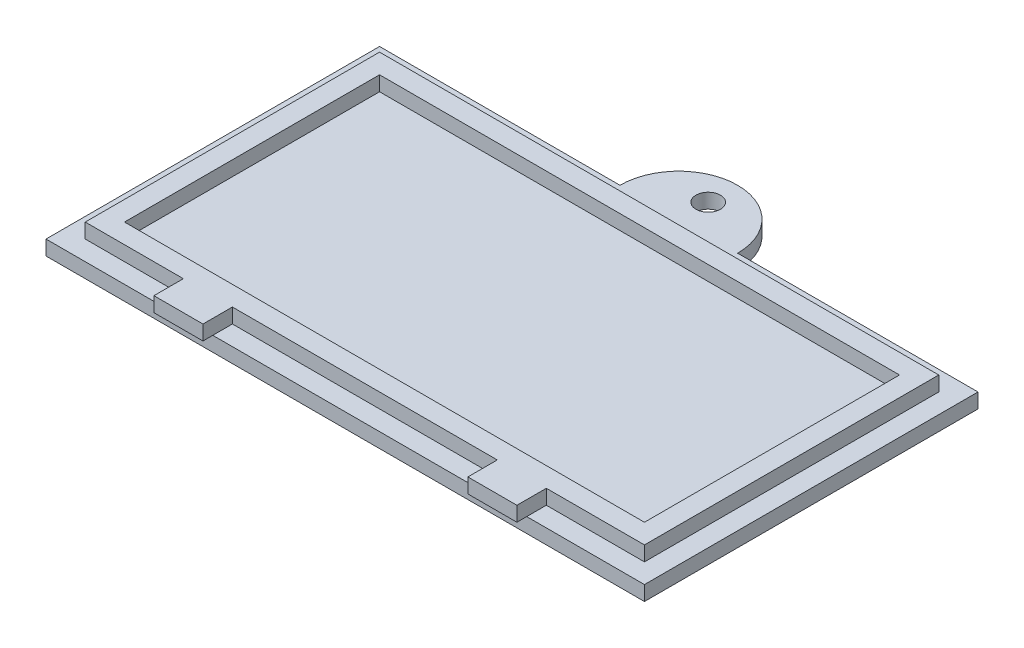
SolidWorks part; units mm, degrees
ref_plane "Front Plane" through (0, 0, 0) normal (0, 0, 1) x (1, 0, 0)
ref_plane "Top Plane" through (0, 0, 0) normal (0, 1, 0) x (1, 0, 0)
ref_plane "Right Plane" through (0, 0, 0) normal (1, 0, 0) x (0, 0, -1)
sketch "Sketch1" plane through (0, 0, 0) normal (0, 1, 0) x (1, 0, 0)
  line L1 (0, 0) -> (61, 0)
  line L2 (0, 0) -> (0, 34)
  line L3 (0, 34) -> (61, 34)
  line L4 (61, 0) -> (61, 34)
  dimension "D1" = 61
  dimension "D2" = 34
extrude "Boss-Extrude1" add sketch "Sketch1" along normal blind 1.5
sketch "Sketch2" plane through (0, 1.5, 0) normal (0, 1, 0) x (1, 0, 0)
  line L0 (61, 34) -> (0, 34) construction
  line L1 (2, 32) -> (59, 32)
  line L2 (2, 32) -> (2, 2)
  line L3 (2, 2) -> (59, 2)
  line L4 (59, 32) -> (59, 2)
  line L5 (0, 34) -> (0, 0) construction
  line L6 (0, 0) -> (61, 0) construction
  line L7 (61, 0) -> (61, 34) construction
  dimension "D1" = 2
  dimension "D2" = 2
  dimension "D3" = 2
  dimension "D4" = 2
extrude "Boss-Extrude2" add sketch "Sketch2" along normal blind 1.5
sketch "Sketch3" plane through (0, 3, 0) normal (0, 1, 0) x (1, 0, 0)
  line L0 (59, 32) -> (2, 32) construction
  line L1 (4, 30) -> (57, 30)
  line L2 (4, 30) -> (4, 4)
  line L3 (4, 4) -> (57, 4)
  line L4 (57, 30) -> (57, 4)
  line L5 (2, 2) -> (59, 2) construction
  line L6 (2, 32) -> (2, 2) construction
  line L7 (59, 2) -> (59, 32) construction
  dimension "D1" = 2
  dimension "D2" = 2
  dimension "D3" = 2
  dimension "D4" = 2
extrude "Cut-Extrude1" cut sketch "Sketch3" against normal blind 1.5
sketch "Sketch4" plane through (0, 0, 0) normal (0, -1, 0) x (-1, 0, 0)
  line L0 (-61, 34) -> (0, 34) construction
  circle A0 centre (-30.5, 34) radius 6
  dimension "D1" = 12
extrude "Boss-Extrude3" add sketch "Sketch4" against normal blind 1.5 contours A0
hole_wizard "M3 Tapped Hole1" [suppressed] positions "3DSketch2" profile "Sketch6" tap size "M3" standard "DIN"
sketch3d "3DSketch2"
  line L0 (27.5, 1.5, -30) -> (27.5, 0, -30) construction
  point P0 (27.5, 0, -30)
sketch "Sketch6" plane through (27.5, 0, -30) normal (1, 0, 0) x (0, 0, -1)
  line L0 (0, 0) -> (0, 8.2511)
  line L1 (0, 8.2511) -> (1.25, 7.5)
  line L2 (1.25, 7.5) -> (1.25, 0)
  line L5 (1.25, 0) -> (0, 0)
  line L10 (0, 8.2511) -> (-1.25, 7.5) construction
  line L11 (0, -6.35) -> (0, 107.95) construction
  dimension "Tap Drill Dia." = 2.5
  dimension "Tap Drill Depth" = 7.5
  dimension "Drill Angle" = 118
cosmetic thread "Hole Thread1" [suppressed] parameters "D1"=6, "D2"=3
sketch "Sketch7" plane through (0, 0, 0) normal (0, -1, 0) x (1, 0, 0)
  point P0 (30.5, -37)
  dimension "D1" = 6
  dimension "D2" = 3
hole_wizard "M3 Tapped Hole2" positions "3DSketch3" profile "Sketch8" tap size "M3" standard "DIN"
sketch3d "3DSketch3"
  point P0 (30.5, 0, -37)
sketch "Sketch8" plane through (30.5, 0, -37) normal (1, 0, 0) x (0, 0, -1)
  line L0 (0, 0) -> (0, 8.2511)
  line L1 (0, 8.2511) -> (1.25, 7.5)
  line L2 (1.25, 7.5) -> (1.25, 0)
  line L5 (1.25, 0) -> (0, 0)
  line L10 (0, 8.2511) -> (-1.25, 7.5) construction
  line L11 (0, -6.35) -> (0, 107.95) construction
  dimension "Tap Drill Dia." = 2.5
  dimension "Tap Drill Depth" = 7.5
  dimension "Drill Angle" = 118
cosmetic thread "Hole Thread2" parameters "D1"=6, "D2"=3
sketch "Sketch9" plane through (0, 0, -2) normal (0, 0, 1) x (1, 0, 0)
  line L0 (2, 3) -> (59, 3) construction
  line L1 (12, 3) -> (17, 3)
  line L2 (12, 3) -> (12, 1.5)
  line L3 (12, 1.5) -> (17, 1.5)
  line L4 (17, 3) -> (17, 1.5)
  line L5 (2, 1.5) -> (59, 1.5) construction
  line L6 (59, 3) -> (59, 1.5) construction
  line L7 (44, 3) -> (49, 3)
  line L8 (44, 3) -> (44, 1.5)
  line L9 (44, 1.5) -> (49, 1.5)
  line L10 (49, 3) -> (49, 1.5)
  line L11 (2, 3) -> (2, 1.5) construction
  dimension "D1" = 1.5
  dimension "D2" = 5
  dimension "D3" = 5
  dimension "D4" = 1.5
  dimension "D5" = 10
  dimension "D6" = 10
extrude "Boss-Extrude4" add sketch "Sketch9" along normal blind 3
